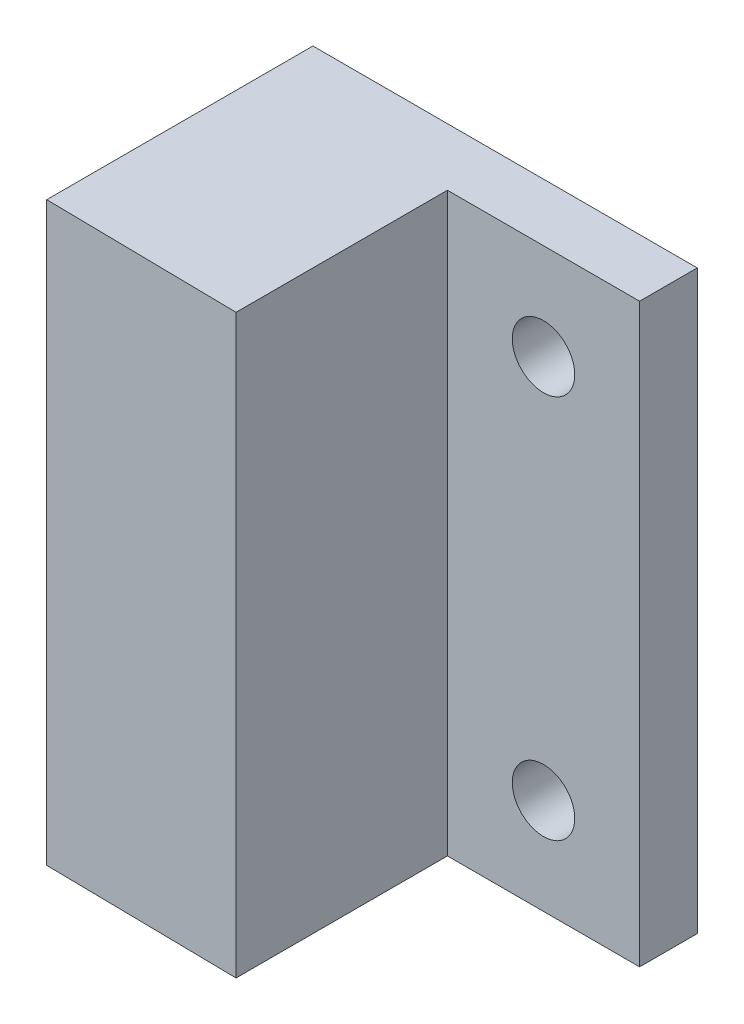
SolidWorks part; units mm, degrees
ref_plane "Plan de face" through (0, 0, 0) normal (0, 0, 1) x (1, 0, 0)
ref_plane "Plan de dessus" through (0, 0, 0) normal (0, 1, 0) x (1, 0, 0)
ref_plane "Plan de droite" through (0, 0, 0) normal (1, 0, 0) x (0, 0, -1)
sketch "Esquisse1" plane through (0, 0, 0) normal (0, 0, 1) x (1, 0, 0)
  line L1 (0, 0) -> (10, 0)
  line L2 (0, 0) -> (0, -30)
  line L3 (0, -30) -> (10, -30)
  line L4 (10, 0) -> (10, -30)
  dimension "D1" = 10
  dimension "D2" = 30
extrude "Boss.-Extru.1" add sketch "Esquisse1" along normal blind 14
sketch "Esquisse2" plane through (10, 0, 0) normal (1, 0, 0) x (0, 0, -1)
  line L0 (-14, -30) -> (0, -30) construction
  line L1 (0, 0) -> (-3, 0)
  line L2 (0, 0) -> (0, -30)
  line L3 (0, -30) -> (-3, -30)
  line L4 (-3, 0) -> (-3, -30)
  dimension "D1" = 3
extrude "Boss.-Extru.2" add sketch "Esquisse2" along normal blind 10
sketch "Esquisse3" plane through (0, 0, 3) normal (0, 0, 1) x (1, 0, 0)
  line L0 (20, 0) -> (10, 0) construction
  line L1 (20, -30) -> (10, -30) construction
  circle A0 centre (15, -5) radius 1.625
  circle A1 centre (15, -25) radius 1.625
  point P6 (15, 0)
  dimension "D1" = 3.25
  dimension "D2" = 3.25
  dimension "D3" = 20
  dimension "D4" = 5
extrude "Enlèv. mat.-Extru.1" cut sketch "Esquisse3" against normal through all
sketch "Esquisse4" plane through (0, -30, 0) normal (0, -1, 0) x (1, 0, 0)
  line L4 (10, 14) -> (0, 14)
  line L5 (0, 14) -> (0, 13.85)
  line L6 (0, 14) -> (0, 0) construction
  line L7 (0, 13.85) -> (10, 14)
  dimension "D1" = 0.15
extrude "Enlèv. mat.-Extru.2" cut sketch "Esquisse4" against normal through all
